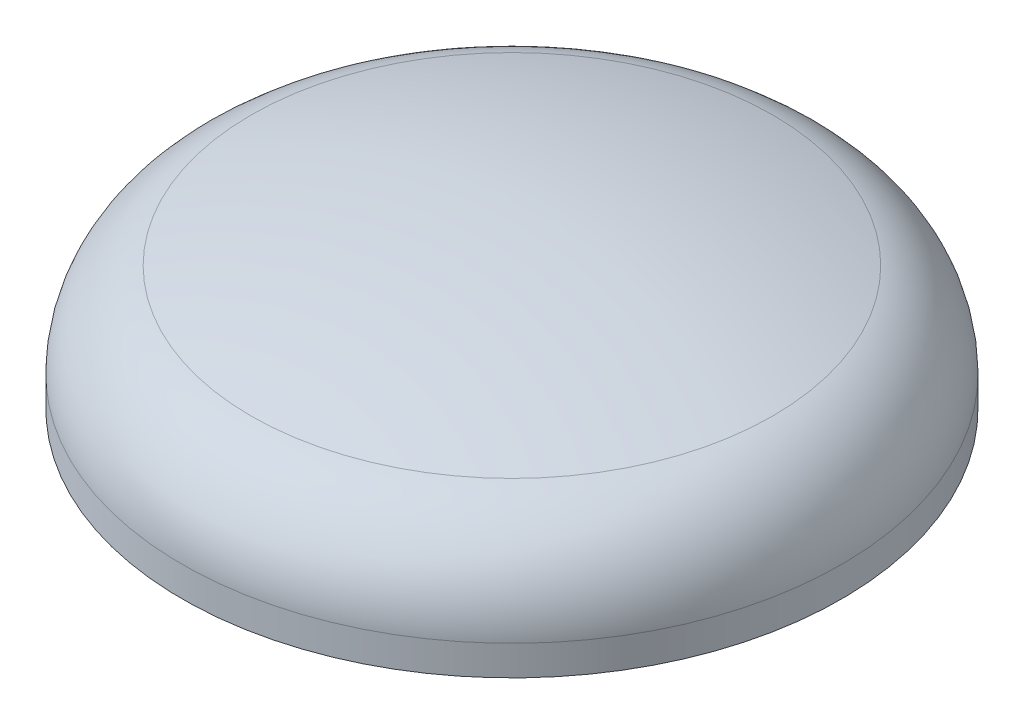
SolidWorks part; units mm, degrees
ref_plane "Front Plane" through (0, 0, 0) normal (0, 0, 1) x (1, 0, 0)
ref_plane "Top Plane" through (0, 0, 0) normal (0, 1, 0) x (1, 0, 0)
ref_plane "Right Plane" through (0, 0, 0) normal (1, 0, 0) x (0, 0, -1)
sketch "Croquis1" plane through (0, 0, 0) normal (1, 0, 0) x (0, 0, -1)
  line L0 (0, 0) -> (0, 0.25)
  line L1 (0, 0) -> (0.5, 0)
  line L2 (0.5, 0) -> (0.5, 0.0454)
  arc A0 (0, 0.25) -> (0.3957, 0.1883) centre (0, -1.05) cw
  arc A1 (0.5, 0.0454) -> (0.3957, 0.1883) centre (0.35, 0.0454) ccw
  point P8 (0.5, 0.15)
  dimension "D4" = 0.15
  dimension "D1" = 0.5
  dimension "D2" = 0.25
  dimension "D3" = 0.15
revolve "Revolución1" add sketch "Croquis1" angle 360 about L0
